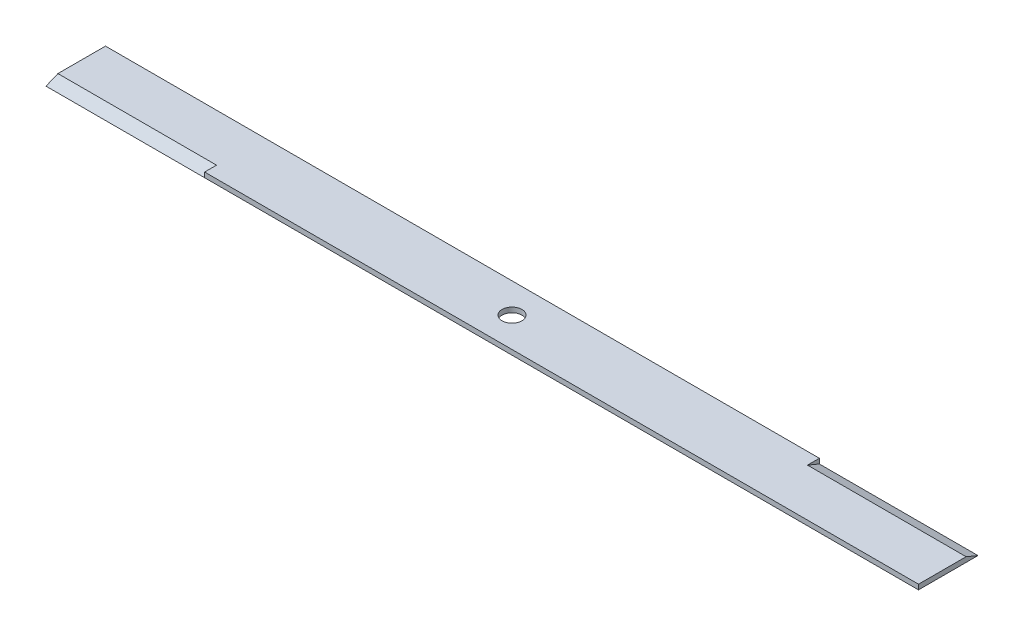
SolidWorks part; units mm, degrees
ref_plane "Front Plane" through (0, 0, 0) normal (0, 0, 1) x (1, 0, 0)
ref_plane "Top Plane" through (0, 0, 0) normal (0, 1, 0) x (1, 0, 0)
ref_plane "Right Plane" through (0, 0, 0) normal (1, 0, 0) x (0, 0, -1)
sketch "Sketch2" plane through (0, 0, 0) normal (0, 1, 0) x (1, 0, 0)
  line L1 (-279.4, 19.05) -> (279.4, 19.05)
  line L2 (-279.4, 19.05) -> (-279.4, -19.05)
  line L3 (-279.4, -19.05) -> (279.4, -19.05)
  line L4 (279.4, 19.05) -> (279.4, -19.05)
  circle A0 centre (0, 0) radius 6.35
  dimension "D3" = 12.7
  dimension "D1" = 558.8
  dimension "D2" = 38.1
  dimension "D4" = 279.4
  dimension "D5" = 19.05
extrude "Mower Blade" add sketch "Sketch2" along normal blind 3.175
sketch "Sketch3" plane through (279.4, 0, 0) normal (1, 0, 0) x (0, 0, -1)
  line L0 (19.05, 0) -> (11.43, 3.175)
  line L1 (-19.05, 3.175) -> (19.05, 3.175) construction
  line L2 (11.43, 3.175) -> (19.05, 3.175)
  line L3 (19.05, 3.175) -> (19.05, 0)
  dimension "D1" = 7.62
extrude "Cutting Edge #1" cut sketch "Sketch3" against normal blind 101.6
sketch "Sketch4" plane through (-279.4, 0, 0) normal (-1, 0, 0) x (0, 0, 1)
  line L0 (19.05, 0) -> (11.43, 3.175)
  line L1 (-19.05, 3.175) -> (19.05, 3.175) construction
  line L2 (11.43, 3.175) -> (19.05, 3.175)
  line L3 (19.05, 3.175) -> (19.05, 0)
  dimension "D1" = 7.62
extrude "Cutting Edge #2" cut sketch "Sketch4" against normal blind 101.6
sketch "Sketch5" plane through (0, 0, 0) normal (0, 1, 0) x (1, 0, 0)
  line L0 (0, 56.7526) -> (0, -61.4092)
extrude "Half model of Blade" [suppressed] cut sketch "Sketch5" against normal through all and the other way through all
